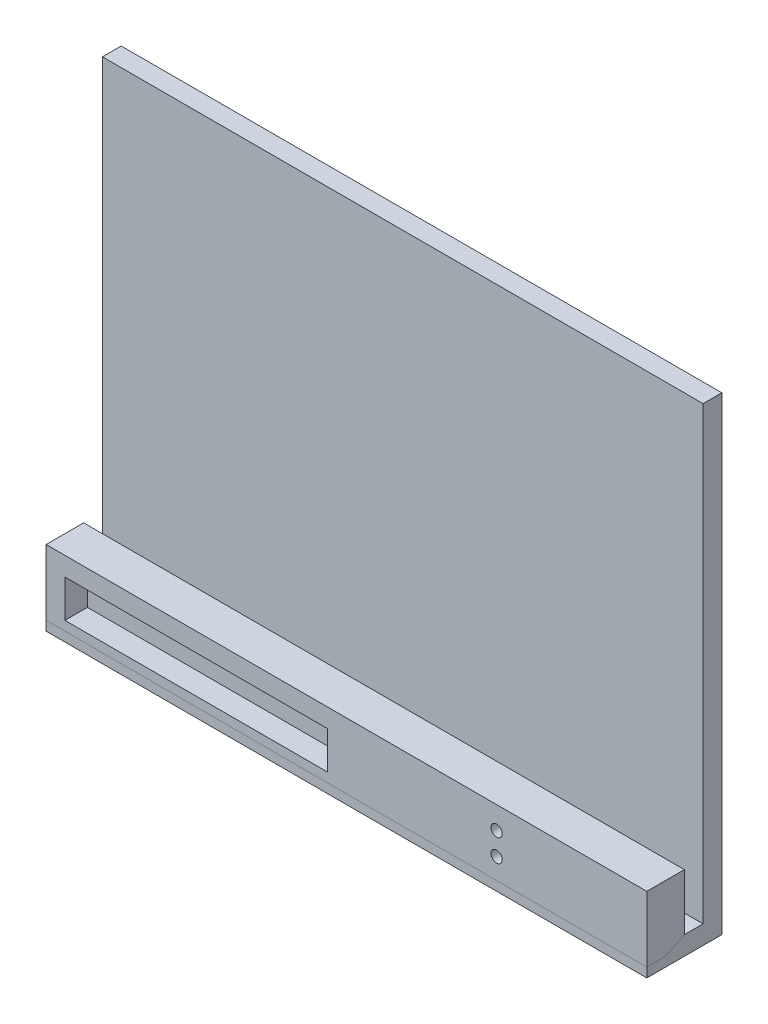
SolidWorks part; units mm, degrees
ref_plane "Front Plane" through (0, 0, 0) normal (0, 0, 1) x (1, 0, 0)
ref_plane "Top Plane" through (0, 0, 0) normal (0, 1, 0) x (1, 0, 0)
ref_plane "Right Plane" through (0, 0, 0) normal (1, 0, 0) x (0, 0, -1)
sketch "Sketch1" plane through (0, 0, 0) normal (0, 0, 1) x (1, 0, 0)
  line L1 (0, 158.75) -> (203.2, 158.75)
  line L2 (0, 158.75) -> (0, 0)
  line L3 (0, 0) -> (203.2, 0)
  line L4 (203.2, 158.75) -> (203.2, 0)
  dimension "D1" = 158.75
  dimension "D2" = 203.2
extrude "Boss-Extrude1" add sketch "Sketch1" along normal blind 6.35
sketch "Sketch2" plane through (0, 0, 6.35) normal (0, 0, 1) x (1, 0, 0)
  line L0 (0, 158.75) -> (0, 0) construction
  line L1 (0, 6.35) -> (203.2, 6.35)
  line L2 (0, 6.35) -> (0, 0)
  line L3 (0, 0) -> (203.2, 0)
  line L4 (203.2, 6.35) -> (203.2, 0)
  dimension "D1" = 6.35
extrude "Boss-Extrude2" add sketch "Sketch2" along normal blind 19.05
sketch "Sketch3" plane through (0, 6.35, 0) normal (0, 1, 0) x (1, 0, 0)
  line L6 (203.2, -25.4) -> (203.2, -6.35) construction
  line L7 (0, -25.4) -> (203.2, -25.4)
  line L8 (0, -25.4) -> (0, -12.7)
  line L9 (0, -12.7) -> (203.2, -12.7)
  line L10 (203.2, -25.4) -> (203.2, -12.7)
  dimension "D1" = 12.7
extrude "Boss-Extrude3" add sketch "Sketch3" along normal blind 19.05
sketch "Sketch4" plane through (0, 0, 25.4) normal (0, 0, 1) x (1, 0, 0)
  line L0 (0, 25.4) -> (0, 0) construction
  line L1 (6.35, 19.05) -> (95.25, 19.05)
  line L2 (6.35, 19.05) -> (6.35, 6.35)
  line L3 (6.35, 6.35) -> (95.25, 6.35)
  line L4 (95.25, 19.05) -> (95.25, 6.35)
  line L5 (0, 25.4) -> (203.2, 25.4) construction
  dimension "D1" = 6.35
  dimension "D2" = 12.7
  dimension "D3" = 6.35
  dimension "D4" = 88.9
extrude "Cut-Extrude1" cut sketch "Sketch4" against normal blind 7.62
sketch "Sketch5" plane through (0, 0, 25.4) normal (0, 0, 1) x (1, 0, 0)
  line L0 (152.4, 25.4) -> (152.4, 0) construction
  line L1 (0, 25.4) -> (203.2, 25.4) construction
  line L2 (0, 0) -> (203.2, 0) construction
  line L3 (203.2, 0) -> (203.2, 25.4) construction
  circle A0 centre (152.4, 17.78) radius 1.905
  circle A1 centre (152.4, 10.16) radius 1.905
  dimension "D1" = 3.81
  dimension "D2" = 3.81
  dimension "D3" = 50.8
  dimension "D4" = 10.16
  dimension "D5" = 7.62
extrude "Cut-Extrude2" cut sketch "Sketch5" against normal up to next
sketch "Sketch6" plane through (203.2, 0, 0) normal (1, 0, 0) x (0, 0, -1)
  line L0 (-25.4, 3.175) -> (-19.05, 3.175)
  line L1 (-25.4, 0) -> (-25.4, 25.4) construction
  line L2 (-19.05, 3.175) -> (-12.7, 6.35)
  line L3 (-25.4, 0) -> (0, 0) construction
  dimension "D1" = 6.35
  dimension "D2" = 3.175
split "Split1" trim tools "Sketch6" bodies to split 105 resulting bodies 111 112
